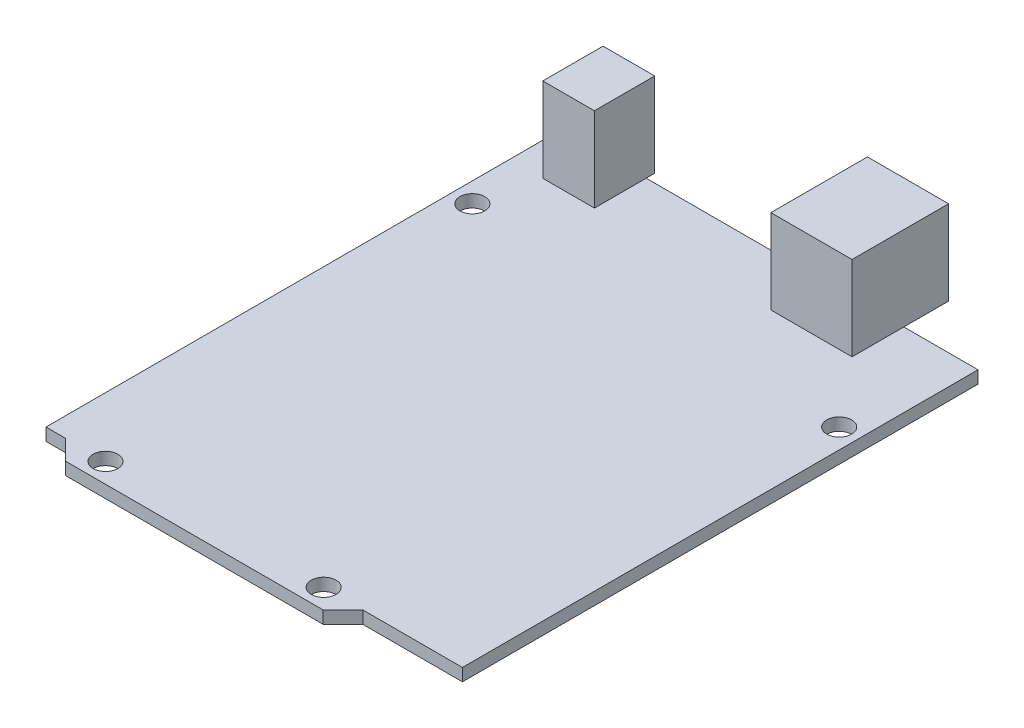
SolidWorks part; units mm, degrees
ref_plane "Front Plane" through (0, 0, 0) normal (0, 0, 1) x (1, 0, 0)
ref_plane "Top Plane" through (0, 0, 0) normal (0, 1, 0) x (1, 0, 0)
ref_plane "Right Plane" through (0, 0, 0) normal (1, 0, 0) x (0, 0, -1)
sketch "Sketch1" plane through (0, 0, 0) normal (0, 1, 0) x (1, 0, 0)
  line L0 (0, 68.58) -> (0, 2.54)
  line L1 (0, 0) -> (53.34, 0) construction
  line L2 (0, 0) -> (0, 68.58) construction
  line L3 (0, 68.58) -> (53.34, 68.58)
  line L4 (53.34, 0) -> (53.34, 68.58) construction
  line L5 (0, 2.54) -> (2.5, 2.54)
  line L6 (2.5, 2.54) -> (5.04, 0)
  line L7 (5.04, 0) -> (38.04, 0)
  line L8 (38.04, 0) -> (40.58, 2.54)
  line L9 (40.58, 2.54) -> (53.34, 2.54)
  line L10 (53.34, 2.54) -> (53.34, 68.58)
  dimension "D1" = 53.34
  dimension "D2" = 68.58
  dimension "D3" = 2.54
  dimension "D4" = 2.5
  dimension "D5" = 45
  dimension "D6" = 45
  dimension "D7" = 33
extrude "Boss-Extrude1" add sketch "Sketch1" along normal blind 1.6
sketch "Sketch2" plane through (0, 1.6, 0) normal (0, 1, 0) x (1, 0, 0)
  line L1 (4.2253, 61.9471) -> (10.8409, 61.9471)
  line L2 (4.2253, 61.9471) -> (4.2253, 69.6654)
  line L3 (4.2253, 69.6654) -> (10.8409, 69.6654)
  line L4 (10.8409, 61.9471) -> (10.8409, 69.6654)
  line L5 (33.4444, 61.9471) -> (43.8404, 61.9471)
  line L6 (33.4444, 61.9471) -> (33.4444, 74.3121)
  line L7 (33.4444, 74.3121) -> (43.8404, 74.3121)
  line L8 (43.8404, 61.9471) -> (43.8404, 74.3121)
extrude "Boss-Extrude2" add sketch "Sketch2" along normal blind 10.8
sketch "Sketch3" plane through (0, 1.6, 0) normal (0, 1, 0) x (1, 0, 0)
  line L0 (2.5, 2.54) -> (40.58, 2.54) construction
  line L2 (53.34, 68.58) -> (43.8404, 68.58) construction
  line L5 (0, 68.58) -> (0, 2.54) construction
  line L6 (4.2253, 68.58) -> (0, 68.58) construction
  circle A0 centre (7.62, 2.54) radius 1.5875
  circle A1 centre (35.56, 2.54) radius 1.5875
  circle A2 centre (50.8, 53.34) radius 1.5875
  circle A3 centre (2.54, 54.61) radius 1.5875
  dimension "D3" = 3.175
  dimension "D1" = 2.54
  dimension "D2" = 13.97
  dimension "D4" = 7.62
  dimension "D5" = 35.56
  dimension "D6" = 15.24
  dimension "D7" = 50.8
extrude "Cut-Extrude1" cut sketch "Sketch3" against normal through all
ref_plane "Plane1" through (26.75, 0, 0) normal (1, 0, 0) x (0, 0, -1)
